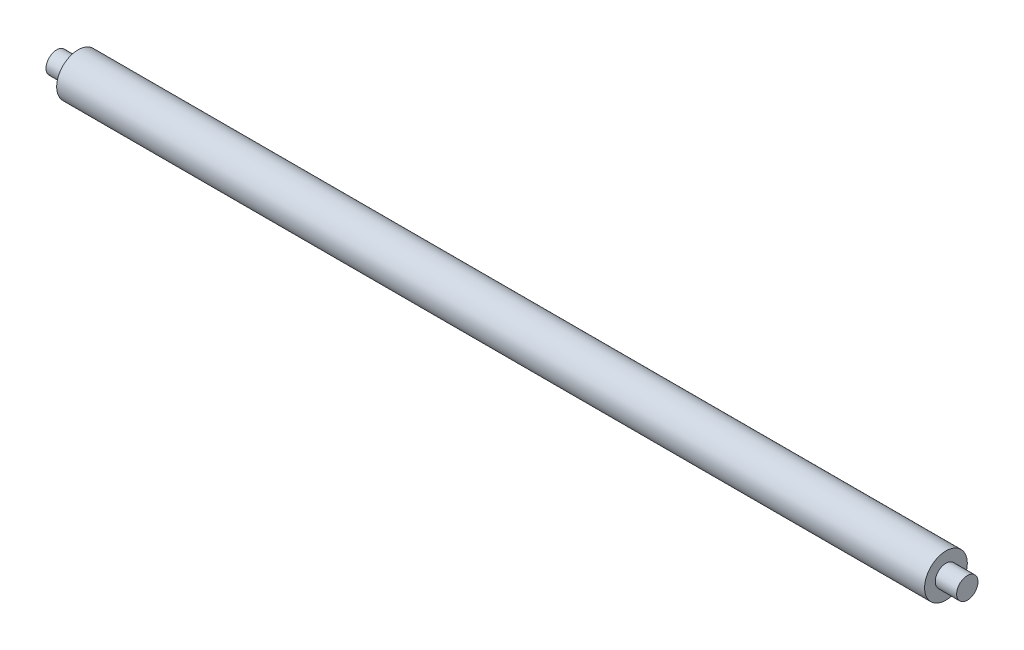
SolidWorks part; units mm, degrees
material "AISI 1020"
ref_plane "Alzado" through (0, 0, 0) normal (0, 0, 1) x (1, 0, 0)
ref_plane "Planta" through (0, 0, 0) normal (0, 1, 0) x (1, 0, 0)
ref_plane "Vista lateral" through (0, 0, 0) normal (1, 0, 0) x (0, 0, -1)
sketch "Croquis1" plane through (0, 0, 0) normal (1, 0, 0) x (0, 0, -1)
  circle A0 centre (0, 0) radius 5
  point P0 (0, 0)
  dimension "D1" = 10
extrude "Saliente-Extruir1" add sketch "Croquis1" along normal mid plane 203
sketch "Croquis2" plane through (0, 0, 0) normal (1, 0, 0) x (0, 0, -1)
  circle A0 centre (0, 0) radius 2.5
  dimension "D1" = 5
extrude "Saliente-Extruir2" add sketch "Croquis2" along normal mid plane 213
